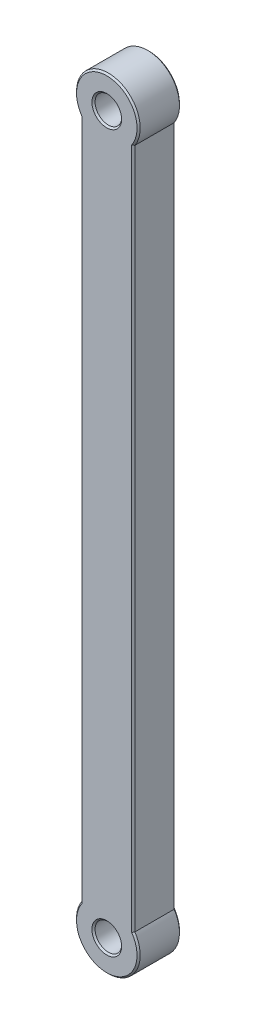
SolidWorks part; units mm, degrees
material "POM 乙缩醛共聚物"
ref_plane "前视基准面" through (0, 0, 0) normal (0, 0, 1) x (1, 0, 0)
ref_plane "上视基准面" through (0, 0, 0) normal (0, 1, 0) x (1, 0, 0)
ref_plane "右视基准面" through (0, 0, 0) normal (1, 0, 0) x (0, 0, -1)
sketch "草图1" plane through (0, 0, 0) normal (0, 0, 1) x (1, 0, 0)
  line L0 (0, 0) -> (0, 135) construction
  line L1 (-5, 0) -> (-5, 135)
  line L2 (5, 0) -> (5, 135)
  arc A0 (-5, 0) -> (5, 0) centre (0, 0) ccw
  arc A1 (5, 135) -> (-5, 135) centre (0, 135) ccw
  point P3 (0, 67.5)
  dimension "D1" = 135
  dimension "D2" = 10
extrude "凸台-拉伸1" add sketch "草图1" along normal blind 8
sketch "草图2" plane through (0, 0, 0) normal (0, 0, 1) x (1, 0, 0)
  circle A0 centre (0, 0) radius 6
  circle A1 centre (0, 135) radius 6
  dimension "D1" = 12
extrude "凸台-拉伸2" add sketch "草图2" along normal up to surface (8 mm away) up to face at (0, 67.5, 8)
sketch "草图3" plane through (0, 0, 0) normal (0, 0, -1) x (-1, 0, 0)
  circle A0 centre (0, 135) radius 2.5
  circle A1 centre (0, 0) radius 2.5
  dimension "D1" = 5
extrude "切除-拉伸1" cut sketch "草图3" against normal through all
chamfer "倒角1" distance 0.3 angle 45 12 edges at (0, -6, 0) (0, -6, 8) (5, 67.5, 0) (0, 141, 8) (0, 141, 0) (-5, 67.5, 0) (-2.5, 0, 0) (-2.5, 135, 0) (5, 67.5, 8) (-5, 67.5, 8) (-2.5, 0, 8) (-2.5, 135, 8)
